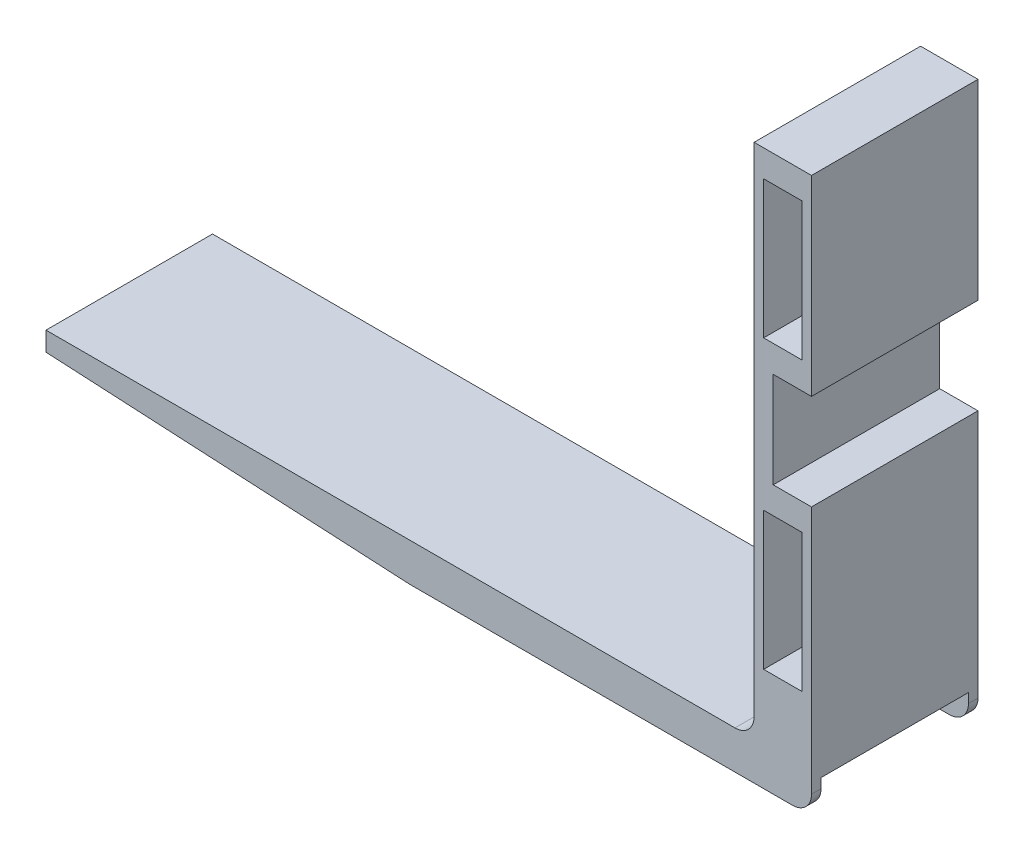
SolidWorks part; units mm, degrees
material "1.0715 (11SMn30)"
ref_plane "Front Plane" through (0, 0, 0) normal (0, 0, 1) x (1, 0, 0)
ref_plane "Top Plane" through (0, 0, 0) normal (0, 1, 0) x (1, 0, 0)
ref_plane "Right Plane" through (0, 0, 0) normal (1, 0, 0) x (0, 0, -1)
sketch "Sketch1" plane through (0, 0, 0) normal (0, 0, 1) x (1, 0, 0)
  line L1 (-202, -150.2941) -> (-202, -140.2941)
  line L3 (198, -150.2941) -> (198, -20.2941)
  line L4 (198, 129.7059) -> (168, 129.7059)
  line L5 (173, -34.2941) -> (193, -34.2941)
  line L6 (173, 115.7059) -> (193, 115.7059)
  line L9 (193, 115.7059) -> (193, 43.7059)
  line L10 (173, 115.7059) -> (173, 43.7059)
  line L11 (173, 43.7059) -> (193, 43.7059)
  line L12 (173, -34.2941) -> (173, -106.2941)
  line L13 (173, -106.2941) -> (193, -106.2941)
  line L14 (193, -34.2941) -> (193, -106.2941)
  line L15 (188, -160.2941) -> (-12, -160.2941)
  line L16 (-12, -160.2941) -> (-202, -150.2941)
  line L17 (198, 29.7059) -> (178, 29.7059)
  line L18 (178, 29.7059) -> (178, -20.2941)
  line L19 (178, -20.2941) -> (198, -20.2941)
  line L20 (198, 29.7059) -> (198, 129.7059)
  line L21 (168, 129.7059) -> (168, -130.2941)
  line L22 (148, -140.2941) -> (-202, -140.2941)
  line L23 (158, -140.2941) -> (148, -140.2941)
  arc A0 (188, -160.2941) -> (198, -150.2941) centre (188, -150.2941) ccw
  arc A2 (168, -130.2941) -> (158, -140.2941) centre (158, -130.2941) cw
  point P8 (185.8157, 79.7059)
  point P11 (185.8157, -70.2941)
  dimension "D13" = 10
  dimension "D1" = 290
  dimension "D2" = 14
  dimension "D3" = 50
  dimension "D4" = 30
  dimension "D5" = 20
  dimension "D6" = 20
  dimension "D7" = 72
  dimension "D8" = 72
  dimension "D9" = 5
  dimension "D10" = 14
  dimension "D11" = 360
  dimension "D12" = 14
  dimension "D14" = 260
  dimension "D15" = 150
  dimension "0.5" = 5
  dimension "D16" = 400
extrude "Boss-Extrude2" add sketch "Sketch1" along normal blind 87
sketch "Sketch2" plane through (-202, 0, 0) normal (-1, 0, 0) x (0, 0, 1)
  line L0 (0, -140.2941) -> (0, -150.2941) construction
  line L2 (5, -145.2941) -> (5, -163.7069)
  line L7 (5, -145.2941) -> (82.0379, -145.2941)
  line L8 (82.0379, -145.2941) -> (82.0379, -163.7069)
  line L9 (82.0379, -163.7069) -> (5, -163.7069)
  line L10 (87, -150.2941) -> (87, -160.2941) construction
  line L11 (87, -140.2941) -> (0, -140.2941) construction
  dimension "D1" = 5
  dimension "D2" = 4.9621
  dimension "D3" = 5
extrude "Cut-Extrude1" cut sketch "Sketch2" against normal blind 420
